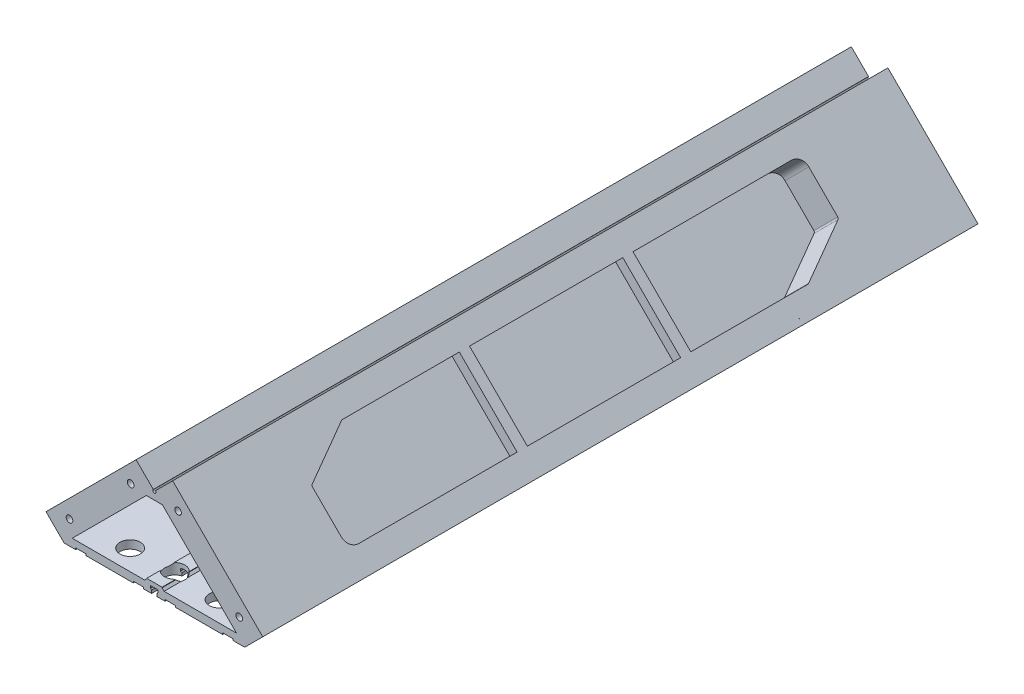
SolidWorks part; units mm, degrees
ref_plane "Front Plane" through (0, 0, 0) normal (0, 0, 1) x (1, 0, 0)
ref_plane "Top Plane" through (0, 0, 0) normal (0, 1, 0) x (1, 0, 0)
ref_plane "Right Plane" through (0, 0, 0) normal (1, 0, 0) x (0, 0, -1)
sketch "Sketch1" plane through (0, 0, 0) normal (0, 0, 1) x (1, 0, 0)
  line L0 (565, 0) -> (590, 0)
  line L1 (0, 0) -> (25, 0)
  line L2 (0, 0) -> (0, 950)
  line L4 (590, 0) -> (590, 950)
  line L5 (25, 55) -> (565, 55)
  line L6 (25, 55) -> (25, 895)
  line L7 (25, 920) -> (565, 920)
  line L8 (565, 55) -> (565, 895)
  line L10 (25, 0) -> (25, 30)
  line L11 (25, 30) -> (565, 30)
  line L12 (565, 0) -> (565, 30)
  line L13 (25, 895) -> (565, 895)
  line L14 (25, 920) -> (25, 950)
  line L15 (312.6777, 1262.6777) -> (630.8757, 944.4796)
  line L16 (295, 1280.3553) -> (312.6777, 1262.6777)
  line L17 (25, 975) -> (295, 1245)
  line L18 (565, 950) -> (565, 975)
  line L19 (565, 950) -> (565, 920)
  line L20 (590, 950) -> (613.1981, 926.8019)
  line L21 (25, 950) -> (25, 975)
  line L22 (295, 1280.3553) -> (277.3223, 1262.6777)
  line L23 (565, 975) -> (295, 1245)
  line L24 (277.3223, 1262.6777) -> (-40.8757, 944.4796)
  line L25 (-40.8757, 944.4796) -> (-23.1981, 926.8019)
  line L26 (0, 950) -> (-23.1981, 926.8019)
  line L27 (613.1981, 926.8019) -> (630.8757, 944.4796)
  line L28 (295, 1280.3553) -> (295, 1004.0858) construction
  point P9 (0, 475)
  dimension "D1" = 590
  dimension "D2" = 950
  dimension "D3" = 25
  dimension "D4" = 25
  dimension "D5" = 30
  dimension "D6" = 25
  dimension "D8" = 25
  dimension "D12" = 450
extrude "Boss-Extrude1" add sketch "Sketch1" along normal blind 25
sketch "Sketch2" plane through (0, 0, 25) normal (0, 0, 1) x (1, 0, 0)
  line L0 (0, 950) -> (0, 0) construction
  line L1 (25, 55) -> (0, 55)
  line L2 (25, 55) -> (25, 30)
  line L3 (25, 30) -> (0, 30)
  line L4 (0, 55) -> (0, 30)
  line L5 (590, 0) -> (590, 950) construction
  line L6 (565, 55) -> (590, 55)
  line L7 (565, 55) -> (565, 30)
  line L8 (565, 30) -> (590, 30)
  line L9 (590, 55) -> (590, 30)
  line L10 (295, 1280.3553) -> (312.6777, 1262.6777)
  line L11 (25, 920) -> (0, 920)
  line L12 (25, 920) -> (25, 895)
  line L13 (25, 895) -> (0, 895)
  line L14 (0, 920) -> (0, 895)
  line L15 (565, 920) -> (590, 920)
  line L16 (565, 920) -> (565, 895)
  line L17 (565, 895) -> (590, 895)
  line L18 (590, 920) -> (590, 895)
  line L20 (295, 1280.3553) -> (277.3223, 1262.6777)
  line L21 (295, 1245) -> (312.6777, 1262.6777)
  line L22 (295, 1245) -> (277.3223, 1262.6777)
  line L23 (295, 1277.5269) -> (309.8492, 1262.6777)
  line L24 (295, 1247.8284) -> (309.8492, 1262.6777)
  line L25 (295, 1247.8284) -> (280.1508, 1262.6777)
  line L26 (295, 1277.5269) -> (280.1508, 1262.6777)
  line L27 (23, 918) -> (2, 918)
  line L28 (2, 918) -> (2, 897)
  line L29 (23, 897) -> (2, 897)
  line L30 (23, 918) -> (23, 897)
  line L31 (567, 918) -> (588, 918)
  line L32 (588, 918) -> (588, 897)
  line L33 (567, 897) -> (588, 897)
  line L34 (567, 918) -> (567, 897)
  line L35 (23, 53) -> (2, 53)
  line L36 (2, 53) -> (2, 32)
  line L37 (23, 32) -> (2, 32)
  line L38 (23, 53) -> (23, 32)
  line L39 (567, 53) -> (588, 53)
  line L40 (588, 53) -> (588, 32)
  line L41 (567, 32) -> (588, 32)
  line L42 (567, 53) -> (567, 32)
  dimension "D1" = 2
  dimension "D2" = 2
  dimension "D3" = 2
  dimension "D4" = 2
  dimension "D5" = 2
extrude "Boss-Extrude2" add sketch "Sketch2" along normal blind 700
sketch "Sketch4" plane through (0, 0, 725) normal (0, 0, 1) x (1, 0, 0)
  line L2 (590, 895) -> (590, 920) construction
  line L9 (565, 895) -> (565, 55) construction
  line L11 (590, 55) -> (590, 895) construction
  line L18 (590, 30) -> (590, 55) construction
  line L21 (565, 30) -> (565, 0) construction
  line L22 (565, 0) -> (590, 0) construction
  line L23 (590, 0) -> (590, 30) construction
  line L25 (565, 55) -> (25, 55) construction
  line L27 (25, 30) -> (565, 30) construction
  line L29 (0, 30) -> (0, 0) construction
  line L30 (0, 0) -> (25, 0) construction
  line L31 (25, 0) -> (25, 30) construction
  line L34 (0, 55) -> (0, 30) construction
  line L41 (0, 895) -> (0, 55) construction
  line L43 (25, 55) -> (25, 895) construction
  line L46 (0, 920) -> (0, 895) construction
  line L53 (565, 920) -> (25, 920) construction
  line L55 (25, 895) -> (565, 895) construction
  line L57 (295, 1245) -> (565, 975) construction
  line L58 (565, 975) -> (565, 920) construction
  line L60 (590, 920) -> (590, 950) construction
  line L61 (590, 950) -> (613.1981, 926.8019) construction
  line L62 (613.1981, 926.8019) -> (630.8757, 944.4796) construction
  line L63 (630.8757, 944.4796) -> (312.6777, 1262.6777) construction
  line L64 (295, 1280.3553) -> (277.3223, 1262.6777) construction
  line L67 (312.6777, 1262.6777) -> (295, 1280.3553) construction
  line L73 (277.3223, 1262.6777) -> (-40.8757, 944.4796) construction
  line L74 (-40.8757, 944.4796) -> (-23.1981, 926.8019) construction
  line L75 (-23.1981, 926.8019) -> (0, 950) construction
  line L76 (0, 950) -> (0, 920) construction
  line L78 (25, 920) -> (25, 975) construction
  line L79 (25, 975) -> (295, 1245) construction
  line L82 (590, 895) -> (590, 920)
  line L89 (565, 895) -> (565, 55)
  line L91 (590, 55) -> (590, 895)
  line L98 (590, 30) -> (590, 55)
  line L101 (565, 30) -> (565, 0)
  line L102 (565, 0) -> (590, 0)
  line L103 (590, 0) -> (590, 30)
  line L105 (565, 55) -> (25, 55)
  line L107 (25, 30) -> (565, 30)
  line L109 (0, 30) -> (0, 0)
  line L110 (0, 0) -> (25, 0)
  line L111 (25, 0) -> (25, 30)
  line L114 (0, 55) -> (0, 30)
  line L121 (0, 895) -> (0, 55)
  line L123 (25, 55) -> (25, 895)
  line L126 (0, 920) -> (0, 895)
  line L133 (565, 920) -> (25, 920)
  line L135 (25, 895) -> (565, 895)
  line L137 (295, 1245) -> (565, 975)
  line L138 (565, 975) -> (565, 920)
  line L140 (590, 920) -> (590, 950)
  line L141 (590, 950) -> (613.1981, 926.8019)
  line L142 (613.1981, 926.8019) -> (630.8757, 944.4796)
  line L143 (630.8757, 944.4796) -> (312.6777, 1262.6777)
  line L144 (295, 1280.3553) -> (277.3223, 1262.6777)
  line L147 (312.6777, 1262.6777) -> (295, 1280.3553)
  line L153 (277.3223, 1262.6777) -> (-40.8757, 944.4796)
  line L154 (-40.8757, 944.4796) -> (-23.1981, 926.8019)
  line L155 (-23.1981, 926.8019) -> (0, 950)
  line L156 (0, 950) -> (0, 920)
  line L158 (25, 920) -> (25, 975)
  line L159 (25, 975) -> (295, 1245)
extrude "Boss-Extrude3" add sketch "Sketch4" along normal blind 25
sketch "Sketch6" plane through (0, 0, 0) normal (0, 0, -1) x (-1, 0, 0)
  line L0 (-25, 895) -> (-25, 55) construction
  line L1 (-25, 255) -> (-29, 255)
  line L2 (-25, 255) -> (-25, 275)
  line L3 (-25, 275) -> (-29, 275)
  line L4 (-29, 255) -> (-29, 275)
  line L5 (-25, 55) -> (-565, 55) construction
  line L6 (-25, 655) -> (-29, 655)
  line L7 (-25, 655) -> (-25, 675)
  line L8 (-25, 675) -> (-29, 675)
  line L9 (-29, 655) -> (-29, 675)
  line L10 (-295, 1280.3553) -> (-295, 1595.1993) construction
  line L11 (-561, 655) -> (-561, 675)
  line L12 (-565, 675) -> (-561, 675)
  line L13 (-565, 655) -> (-565, 675)
  line L14 (-565, 655) -> (-561, 655)
  line L15 (-561, 255) -> (-561, 275)
  line L16 (-565, 275) -> (-561, 275)
  line L17 (-565, 255) -> (-565, 275)
  line L18 (-565, 255) -> (-561, 255)
  dimension "D1" = 4
  dimension "D2" = 4
  dimension "D3" = 20
  dimension "D4" = 20
  dimension "D5" = 200
  dimension "D6" = 600
extrude "Boss-Extrude4" add sketch "Sketch6" against normal up to surface (25 mm away) up to face at (577.5, 475, 25)
sketch "Sketch8" plane through (0, 0, 750) normal (0, 0, 1) x (1, 0, 0)
  line L1 (29, 675) -> (25, 675)
  line L2 (29, 675) -> (29, 655)
  line L3 (29, 655) -> (25, 655)
  line L4 (25, 675) -> (25, 655)
  line L5 (29, 275) -> (25, 275)
  line L6 (29, 275) -> (29, 255)
  line L7 (29, 255) -> (25, 255)
  line L8 (25, 275) -> (25, 255)
  line L9 (561, 275) -> (565, 275)
  line L10 (561, 275) -> (561, 255)
  line L11 (561, 255) -> (565, 255)
  line L12 (565, 275) -> (565, 255)
  line L13 (561, 675) -> (565, 675)
  line L14 (561, 675) -> (561, 655)
  line L15 (561, 655) -> (565, 655)
  line L16 (565, 675) -> (565, 655)
extrude "Boss-Extrude5" add sketch "Sketch8" against normal up to surface (25 mm away) up to face at (577.5, 475, 725)
sketch "Sketch9" plane through (0, 0, 750) normal (0, 0, 1) x (1, 0, 0)
  line L0 (295, 1245) -> (295, 920) construction
  line L1 (561, 255) -> (551, 255)
  line L2 (561, 255) -> (561, 270)
  line L3 (561, 270) -> (559, 270)
  line L4 (551, 255) -> (551, 257)
  line L7 (551, 257) -> (559, 257)
  line L8 (559, 270) -> (559, 257)
  line L9 (561, 655) -> (551, 655)
  line L10 (561, 655) -> (561, 670)
  line L11 (561, 670) -> (559, 670)
  line L12 (551, 655) -> (551, 657)
  line L15 (551, 657) -> (559, 657)
  line L16 (559, 670) -> (559, 657)
  line L17 (25, 920) -> (565, 920) construction
  line L18 (31, 670) -> (31, 657)
  line L19 (39, 657) -> (31, 657)
  line L20 (39, 655) -> (39, 657)
  line L21 (29, 670) -> (31, 670)
  line L22 (29, 655) -> (29, 670)
  line L23 (29, 655) -> (39, 655)
  line L24 (31, 270) -> (31, 257)
  line L25 (39, 257) -> (31, 257)
  line L26 (39, 255) -> (39, 257)
  line L27 (29, 270) -> (31, 270)
  line L28 (29, 255) -> (29, 270)
  line L29 (29, 255) -> (39, 255)
  dimension "D1" = 15
  dimension "D2" = 10
  dimension "D3" = 8
  dimension "D4" = 13
  dimension "D5" = 10
  dimension "D6" = 15
  dimension "D7" = 13
  dimension "D8" = 8
extrude "Boss-Extrude6" add sketch "Sketch9" against normal up to surface (750 mm away) up to face at (295, 537.1476, 0)
sketch "Sketch10" plane through (0, 0, 0) normal (0, -1, 0) x (1, 0, 0)
  circle A0 centre (577.5, 12.5) radius 20
  circle A1 centre (577.5, 737.5) radius 20
  circle A2 centre (12.5, 737.5) radius 20
  circle A3 centre (12.5, 12.5) radius 20
  dimension "D1" = 40
extrude "Boss-Extrude7" add sketch "Sketch10" along normal blind 6
sketch "Sketch11" plane through (0, -6, 0) normal (0, -1, 0) x (1, 0, 0)
  line L0 (295, 25) -> (295, -142.0553) construction
  line L1 (591.3227, 25.9794) -> (563.3227, 25.9794)
  line L2 (591.3227, 25.9794) -> (591.3227, -19.0206)
  line L3 (591.3227, -19.0206) -> (563.3227, -19.0206)
  line L4 (563.3227, 25.9794) -> (563.3227, -19.0206)
  line L5 (563.3227, 724.0206) -> (563.3227, 769.0206)
  line L6 (591.3227, 769.0206) -> (563.3227, 769.0206)
  line L10 (591.3227, 724.0206) -> (591.3227, 769.0206)
  line L11 (591.3227, 724.0206) -> (563.3227, 724.0206)
  line L12 (25, 25) -> (565, 25) construction
  line L13 (-1.3227, 724.0206) -> (26.6773, 724.0206)
  line L14 (-1.3227, 724.0206) -> (-1.3227, 769.0206)
  line L15 (-1.3227, 769.0206) -> (26.6773, 769.0206)
  line L16 (26.6773, 724.0206) -> (26.6773, 769.0206)
  line L17 (26.6773, 25.9794) -> (26.6773, -19.0206)
  line L18 (-1.3227, -19.0206) -> (26.6773, -19.0206)
  line L19 (-1.3227, 25.9794) -> (-1.3227, -19.0206)
  line L20 (-1.3227, 25.9794) -> (26.6773, 25.9794)
  dimension "D1" = 28
  dimension "D2" = 45
extrude "Boss-Extrude8" add sketch "Sketch11" along normal blind 2
sketch "Sketch12" plane through (0, -8, 0) normal (0, -1, 0) x (1, 0, 0)
  line L0 (591.3227, -19.0206) -> (591.3227, 25.9794) construction
  line L1 (591.3227, 25.9794) -> (589.3227, 25.9794)
  line L2 (591.3227, 25.9794) -> (591.3227, -19.0206)
  line L3 (591.3227, -19.0206) -> (589.3227, -19.0206)
  line L4 (589.3227, 25.9794) -> (589.3227, -19.0206)
  line L5 (591.3227, 25.9794) -> (563.3227, 25.9794) construction
  line L6 (563.3227, -19.0206) -> (591.3227, -19.0206) construction
  line L7 (590, 375) -> (666.7181, 375) construction
  line L8 (563.3227, 25.9794) -> (565.3227, 25.9794)
  line L9 (563.3227, 25.9794) -> (563.3227, -19.0206)
  line L10 (563.3227, -19.0206) -> (565.3227, -19.0206)
  line L11 (565.3227, 25.9794) -> (565.3227, -19.0206)
  line L13 (24.6773, 25.9794) -> (24.6773, -19.0206)
  line L14 (26.6773, -19.0206) -> (24.6773, -19.0206)
  line L15 (26.6773, 25.9794) -> (26.6773, -19.0206)
  line L16 (26.6773, 25.9794) -> (24.6773, 25.9794)
  line L17 (0.6773, 25.9794) -> (0.6773, -19.0206)
  line L18 (-1.3227, -19.0206) -> (0.6773, -19.0206)
  line L19 (-1.3227, 25.9794) -> (-1.3227, -19.0206)
  line L20 (-1.3227, 25.9794) -> (0.6773, 25.9794)
  line L21 (590, 725) -> (590, 25) construction
  line L22 (-1.3227, 724.0206) -> (0.6773, 724.0206)
  line L23 (-1.3227, 724.0206) -> (-1.3227, 769.0206)
  line L24 (-1.3227, 769.0206) -> (0.6773, 769.0206)
  line L25 (0.6773, 724.0206) -> (0.6773, 769.0206)
  line L26 (26.6773, 724.0206) -> (24.6773, 724.0206)
  line L27 (26.6773, 724.0206) -> (26.6773, 769.0206)
  line L28 (26.6773, 769.0206) -> (24.6773, 769.0206)
  line L29 (24.6773, 724.0206) -> (24.6773, 769.0206)
  line L30 (565.3227, 724.0206) -> (565.3227, 769.0206)
  line L31 (563.3227, 769.0206) -> (565.3227, 769.0206)
  line L32 (563.3227, 724.0206) -> (563.3227, 769.0206)
  line L33 (563.3227, 724.0206) -> (565.3227, 724.0206)
  line L34 (589.3227, 724.0206) -> (589.3227, 769.0206)
  line L35 (591.3227, 769.0206) -> (589.3227, 769.0206)
  line L36 (591.3227, 724.0206) -> (591.3227, 769.0206)
  line L37 (591.3227, 724.0206) -> (589.3227, 724.0206)
  dimension "D1" = 2
  dimension "D2" = 2
extrude "Boss-Extrude9" add sketch "Sketch12" along normal blind 38
sketch "Sketch13" plane through (591.3227, 0, 0) normal (1, 0, 0) x (0, 0, -1)
  line L0 (-25.9794, -6) -> (9.0206, -46)
  line L1 (19.0206, -46) -> (-25.9794, -46) construction
  line L2 (19.0206, -46) -> (19.0206, -6) construction
  line L3 (9.0206, -46) -> (-32.8867, -57.1167)
  line L4 (-32.8867, -57.1167) -> (-25.9794, -6)
  line L5 (-375, 30) -> (-375, -46) construction
  line L6 (-725, 30) -> (-25, 30) construction
  line L7 (-717.1133, -57.1167) -> (-724.0206, -6)
  line L8 (-759.0206, -46) -> (-717.1133, -57.1167)
  line L9 (-724.0206, -6) -> (-759.0206, -46)
  dimension "D1" = 10
extrude "Cut-Extrude1" cut sketch "Sketch13" against normal through all
fillet "Fillet1" radius 6 16 edges at (590.3227, -46, 759.0206) (590.3227, -46, 769.0206) (-0.3227, -46, -9.0206) (-0.3227, -46, -19.0206) (25.6773, -46, -19.0206) (25.6773, -46, -9.0206) (25.6773, -46, 759.0206) (-0.3227, -46, 759.0206) (-0.3227, -46, 769.0206) (25.6773, -46, 769.0206) (564.3227, -46, 759.0206) (564.3227, -46, 769.0206) (590.3227, -46, -19.0206) (564.3227, -46, -19.0206) (564.3227, -46, -9.0206) (590.3227, -46, -9.0206)
sketch "Sketch14" plane through (565.3227, 0, 0) normal (1, 0, 0) x (0, 0, -1)
  circle A0 centre (13.0206, -40) radius 25
  circle A1 centre (-763.0206, -40) radius 25
  dimension "D1" = 50
  dimension "D2" = 50
extrude "Boss-Extrude10" add sketch "Sketch14" along normal up to surface (24 mm away) up to face at (589.3227, -32.2803, -7.8041)
sketch "Sketch15" plane through (24.6773, 0, 0) normal (-1, 0, 0) x (0, 0, 1)
  circle A0 centre (763.0206, -40) radius 25
  circle A1 centre (-13.0206, -40) radius 25
extrude "Boss-Extrude11" add sketch "Sketch15" along normal up to surface (24 mm away) up to face at (0.6773, -32.2803, -7.8041)
sketch "Sketch18" plane through (0, 0, 25) normal (0, 0, 1) x (1, 0, 0)
  line L0 (277.1102, 1262.4655) -> (188.934, 1174.2893)
  line L1 (295, 1280.3553) -> (-40.8757, 944.4796) construction
  line L2 (312.8898, 1262.4655) -> (401.066, 1174.2893)
  line L3 (293.9393, 1245.6364) -> (277.1102, 1262.4655)
  line L4 (630.8757, 944.4796) -> (295, 1280.3553) construction
  line L5 (401.066, 1174.2893) -> (383.3883, 1156.6117)
  line L6 (565, 975) -> (295, 1245) construction
  line L7 (188.934, 1174.2893) -> (206.6117, 1156.6117)
  line L8 (295, 1245) -> (25, 975) construction
  line L9 (206.6117, 1156.6117) -> (383.3883, 1156.6117)
  line L10 (277.1102, 1255.3945) -> (196.0051, 1174.2893)
  line L11 (196.0051, 1174.2893) -> (205.6827, 1164.6117)
  line L12 (296.0607, 1245.6364) -> (312.8898, 1262.4655)
  line L14 (393.9949, 1174.2893) -> (384.3173, 1164.6117)
  line L15 (312.8898, 1255.3945) -> (393.9949, 1174.2893)
  line L16 (295, 1237.5047) -> (312.8898, 1255.3945)
  line L17 (295, 1237.5047) -> (277.1102, 1255.3945)
  line L18 (196.0051, 1174.2893) -> (208.6827, 1161.6117) construction
  line L19 (384.3173, 1164.6117) -> (205.6827, 1164.6117)
  line L20 (393.9949, 1174.2893) -> (381.3173, 1161.6117) construction
  line L21 (208.6827, 1161.6117) -> (381.3173, 1161.6117) construction
  line L22 (295, 1244.5757) -> (312.8898, 1262.4655) construction
  line L23 (295, 1244.5757) -> (277.1102, 1262.4655) construction
  arc A0 (293.9393, 1245.6364) -> (296.0607, 1245.6364) centre (295, 1244.5757) ccw
  dimension "D2" = 3
  dimension "D1" = 5
extrude "Boss-Extrude13" add sketch "Sketch18" along normal up to surface (700 mm away) up to face at (520.2189, 1017.9949, 725)
sketch "Sketch19" plane through (0, 0, 0) normal (0, 0, -1) x (-1, 0, 0)
  line L0 (-401.066, 1174.2893) -> (-312.8898, 1262.4655)
  line L1 (-312.8898, 1262.4655) -> (-296.0607, 1245.6364)
  line L2 (-293.9393, 1245.6364) -> (-277.1102, 1262.4655)
  line L3 (-277.1102, 1262.4655) -> (-188.934, 1174.2893)
  line L4 (-188.934, 1174.2893) -> (-206.6117, 1156.6117)
  line L5 (-206.6117, 1156.6117) -> (-383.3883, 1156.6117)
  line L6 (-383.3883, 1156.6117) -> (-401.066, 1174.2893)
  arc A0 (-296.0607, 1245.6364) -> (-293.9393, 1245.6364) centre (-295, 1244.5757) ccw
extrude "Cut-Extrude2" cut sketch "Sketch19" against normal through all flip side to cut
sketch "Sketch20" plane through (0, 0, 0) normal (0, 0, -1) x (-1, 0, 0)
  circle A0 centre (-293.0221, 1200.6008) radius 150.3669
extrude "Cut-Extrude3" cut sketch "Sketch20" against normal blind 25
sketch "Sketch21" plane through (0, 0, 750) normal (0, 0, 1) x (1, 0, 0)
  circle A0 centre (288.0844, 1190.2881) radius 126.6007
extrude "Cut-Extrude4" cut sketch "Sketch21" against normal blind 25
sketch "Sketch22" plane through (0, 0, 0) normal (0, 0, 1) x (1, 0, 0)
  circle A0 centre (322.4016, 0) radius 452.2192
extrude "Cut-Extrude5" cut sketch "Sketch22" against normal through all
sketch "Sketch25" plane through (0, 0, 25) normal (0, 0, -1) x (-1, 0, 0)
  line L0 (-295, 1237.5047) -> (-295, 1156.6117) construction
  line L1 (-206.6117, 1156.6117) -> (-383.3883, 1156.6117) construction
  line L16 (-371.9832, 1155.1117) -> (-361.7832, 1155.1117)
  line L17 (-371.9832, 1155.1117) -> (-371.9832, 1158.1117)
  line L18 (-371.9832, 1158.1117) -> (-361.7832, 1158.1117)
  line L19 (-361.7832, 1155.1117) -> (-361.7832, 1158.1117)
  line L31 (-315.6596, 1155.1117) -> (-305.4596, 1155.1117)
  line L32 (-315.6596, 1155.1117) -> (-315.6596, 1158.1117)
  line L33 (-315.6596, 1158.1117) -> (-305.4596, 1158.1117)
  line L34 (-305.4596, 1155.1117) -> (-305.4596, 1158.1117)
  line L38 (-284.5404, 1155.1117) -> (-284.5404, 1158.1117)
  line L39 (-274.3404, 1158.1117) -> (-284.5404, 1158.1117)
  line L40 (-274.3404, 1155.1117) -> (-274.3404, 1158.1117)
  line L41 (-274.3404, 1155.1117) -> (-284.5404, 1155.1117)
  line L42 (-228.2168, 1155.1117) -> (-228.2168, 1158.1117)
  line L43 (-218.0168, 1158.1117) -> (-228.2168, 1158.1117)
  line L44 (-218.0168, 1155.1117) -> (-218.0168, 1158.1117)
  line L45 (-218.0168, 1155.1117) -> (-228.2168, 1155.1117)
  dimension "D1" = 10.2
  dimension "D2" = 10.2
  dimension "D3" = 3
  dimension "D4" = 3
extrude "Cut-Extrude7" cut sketch "Sketch25" against normal through all
sketch "Sketch28" plane through (0, 0, 25) normal (0, 0, -1) x (-1, 0, 0)
  line L0 (-284.5404, 1156.6117) -> (-305.4596, 1156.6117) construction
  line L5 (-297.7, 1153.4117) -> (-292.3, 1153.4117)
  line L6 (-292.3, 1153.4117) -> (-292.3, 1159.5288)
  line L12 (-292.3, 1159.5288) -> (-291.3, 1160.5288)
  line L13 (-291.3, 1160.5288) -> (-291.3, 1162.8117)
  line L15 (-291.3, 1162.8117) -> (-298.7, 1162.8117)
  line L16 (-298.7, 1160.5288) -> (-298.7, 1162.8117)
  line L17 (-297.7, 1159.5288) -> (-298.7, 1160.5288)
  line L18 (-297.7, 1153.4117) -> (-297.7, 1159.5288)
  point P0 (-295, 1156.6117)
  point P7 (-295, 1159.6117)
extrude "Cut-Extrude8" cut sketch "Sketch28" against normal through all
sketch "Sketch32" plane through (0, 0, 25) normal (0, 0, -1) x (-1, 0, 0)
  line L0 (-205.6827, 1164.6117) -> (-384.3173, 1164.6117) construction
  line L1 (-302.5, 1167.1117) -> (-287.5, 1167.1117)
  line L2 (-302.5, 1167.1117) -> (-302.5, 1164.6117)
  line L4 (-287.5, 1167.1117) -> (-287.5, 1164.6117)
  line L5 (-302.5, 1167.1117) -> (-295, 1164.6117) construction
  line L6 (-295, 1164.6117) -> (-287.5, 1167.1117) construction
  line L7 (-302.5, 1164.6117) -> (-287.5, 1164.6117)
  point P0 (-295, 1164.6117)
  dimension "D1" = 15
extrude "Boss-Extrude15" add sketch "Sketch32" against normal up to surface (700 mm away) up to face at (295, 1171.006, 725)
chamfer "Chamfer1" distance 2 angle 45 1 edges at (302.5, 1164.6117, 375)
chamfer "Chamfer2" distance 2 angle 45 1 edges at (287.5, 1164.6117, 375)
sketch "Sketch36" plane through (0, 0, 25) normal (0, 0, -1) x (-1, 0, 0)
  line L0 (-291.204, 1245.1087) -> (-287.5, 1245.1087)
  line L5 (-302.5, 1245.1087) -> (-298.796, 1245.1087)
  line L6 (-302.5, 1245.1087) -> (-302.5, 1237.1087)
  line L7 (-302.5, 1237.1087) -> (-287.5, 1237.1087)
  line L8 (-287.5, 1245.1087) -> (-287.5, 1237.1087)
  line L9 (-298.4776, 1242.9634) -> (-294.4016, 1240.7895) construction
  line L10 (-295.5984, 1240.7895) -> (-287.5, 1245.1087) construction
  arc A0 (-298.796, 1245.1087) -> (-291.204, 1245.1087) centre (-295, 1244.5757) ccw
  point P0 (-295, 1241.1087)
  dimension "D1" = 15
  dimension "D2" = 8
extrude "Boss-Extrude16" add sketch "Sketch36" against normal up to surface (700 mm away) up to face at (295, 1171.006, 725)
sketch "Sketch38" plane through (787.6777, 787.6777, 0) normal (0.7071, 0.7071, 0) x (0, 0, -1)
  line L0 (-725, 671.4514) -> (-25, 671.4514) construction
  line L1 (-575, 649.4514) -> (-135, 649.4514)
  line L2 (-625, 620.5839) -> (-625, 579.4514)
  line L3 (-615, 569.4514) -> (-175, 569.4514)
  line L4 (-125, 639.4514) -> (-125, 598.319)
  line L6 (-575, 649.4514) -> (-625, 620.5839)
  line L7 (-125, 598.319) -> (-175, 569.4514)
  arc A0 (-125, 639.4514) -> (-135, 649.4514) centre (-135, 639.4514) ccw
  arc A1 (-615, 569.4514) -> (-625, 579.4514) centre (-615, 579.4514) cw
  dimension "D2" = 10
  dimension "D1" = 100
  dimension "D4" = 22
  dimension "D5" = 30
  dimension "D8" = 30
extrude "Cut-Extrude12" cut sketch "Sketch38" against normal blind 6
sketch "Sketch39" plane through (787.6777, 787.6777, 0) normal (0.7071, 0.7071, 0) x (0, 0, -1)
  line L0 (-125, 598.319) -> (-125, 639.4514) construction
  line L1 (-175, 569.4514) -> (-125, 598.319) construction
  line L2 (-615, 569.4514) -> (-175, 569.4514) construction
  line L3 (-625, 620.5839) -> (-625, 579.4514) construction
  line L4 (-575, 649.4514) -> (-625, 620.5839) construction
  line L5 (-135, 649.4514) -> (-575, 649.4514) construction
  line L6 (-125, 598.319) -> (-125, 639.4514)
  line L7 (-175, 569.4514) -> (-125, 598.319)
  line L8 (-615, 569.4514) -> (-175, 569.4514)
  line L9 (-625, 620.5839) -> (-625, 579.4514)
  line L10 (-575, 649.4514) -> (-625, 620.5839)
  line L11 (-135, 649.4514) -> (-575, 649.4514)
  line L12 (-121, 596.0096) -> (-121, 639.4514)
  line L13 (-135, 653.4514) -> (-576.0718, 653.4514)
  line L14 (-576.0718, 653.4514) -> (-629, 622.8933)
  line L15 (-629, 622.8933) -> (-629, 579.4514)
  line L16 (-615, 565.4514) -> (-173.9282, 565.4514)
  line L17 (-173.9282, 565.4514) -> (-121, 596.0096)
  arc A0 (-125, 639.4514) -> (-135, 649.4514) centre (-135, 639.4514) ccw construction
  arc A1 (-625, 579.4514) -> (-615, 569.4514) centre (-615, 579.4514) ccw construction
  arc A2 (-125, 639.4514) -> (-135, 649.4514) centre (-135, 639.4514) ccw
  arc A3 (-625, 579.4514) -> (-615, 569.4514) centre (-615, 579.4514) ccw
  arc A4 (-121, 639.4514) -> (-135, 653.4514) centre (-135, 639.4514) ccw
  arc A5 (-629, 579.4514) -> (-615, 565.4514) centre (-615, 579.4514) ccw
  dimension "D1" = 4
extrude "Boss-Extrude17" add sketch "Sketch39" against normal blind 33
sketch "Sketch40" plane through (764.3431, 764.3431, 0) normal (-0.7071, -0.7071, 0) x (0, 0, 1)
  line L6 (172.8652, 566.0652) -> (619.0997, 566.0652)
  line L7 (629, 579.4514) -> (629, 622.8933)
  line L8 (629, 622.8933) -> (576.0718, 653.4514)
  line L9 (576.0718, 653.4514) -> (135, 653.4514)
  line L10 (121, 639.4514) -> (121, 596.0096)
  line L11 (121, 596.0096) -> (172.8652, 566.0652)
  line L12 (172.8652, 566.0652) -> (619.0997, 566.0652)
  line L13 (629, 579.4514) -> (629, 622.8933)
  line L14 (629, 622.8933) -> (576.0718, 653.4514)
  line L15 (576.0718, 653.4514) -> (135, 653.4514)
  line L16 (121, 639.4514) -> (121, 596.0096)
  line L17 (121, 596.0096) -> (172.8652, 566.0652)
  arc A2 (619.0997, 566.0652) -> (629, 579.4514) centre (615, 579.4514) ccw
  arc A3 (135, 653.4514) -> (121, 639.4514) centre (135, 639.4514) ccw
  arc A4 (619.0997, 566.0652) -> (629, 579.4514) centre (615, 579.4514) ccw
  arc A5 (135, 653.4514) -> (121, 639.4514) centre (135, 639.4514) ccw
  dimension "D1" = 0
extrude "Boss-Extrude18" add sketch "Sketch40" along normal blind 4
fillet "Fillet2" radius 2 4 edges at (373.3474, 1178.6734, 175) (352.935, 1199.0858, 125) (316.7789, 1235.2419, 575) (337.1913, 1214.8295, 625)
sketch "Sketch42" plane through (-492.6777, 492.6777, 0) normal (-0.7071, 0.7071, 0) x (0, 0, 1)
  line L1 (175, 1066.6444) -> (615, 1066.6444)
  line L2 (125, 1037.7769) -> (125, 996.6444)
  line L3 (135, 986.6444) -> (575, 986.6444)
  line L4 (625, 1056.6444) -> (625, 1015.512)
  line L5 (25, 963.9444) -> (25, 1088.6444) construction
  line L6 (175, 1066.6444) -> (125, 1037.7769)
  line L7 (625, 1015.512) -> (575, 986.6444)
  line L9 (725, 1088.6444) -> (25, 1088.6444) construction
  arc A0 (625, 1056.6444) -> (615, 1066.6444) centre (615, 1056.6444) ccw
  arc A1 (135, 986.6444) -> (125, 996.6444) centre (135, 996.6444) cw
  dimension "D2" = 10
  dimension "D1" = 440
  dimension "D3" = 80
  dimension "D4" = 500
  dimension "D5" = 30
  dimension "D6" = 57.735
  dimension "D7" = 100
  dimension "D8" = 30
  dimension "D9" = 22
extrude "Cut-Extrude13" cut sketch "Sketch42" against normal blind 10
sketch "Sketch43" plane through (-492.6777, 492.6777, 0) normal (-0.7071, 0.7071, 0) x (0, 0, 1)
  line L0 (615, 1070.6444) -> (173.9282, 1070.6444)
  line L1 (173.9282, 1070.6444) -> (121, 1040.0863)
  line L2 (121, 1040.0863) -> (121, 996.6444)
  line L3 (135, 982.6444) -> (576.0718, 982.6444)
  line L4 (576.0718, 982.6444) -> (629, 1013.2026)
  line L5 (629, 1013.2026) -> (629, 1056.6444)
  line L6 (615, 1066.6444) -> (175, 1066.6444)
  line L7 (625, 1015.512) -> (625, 1056.6444)
  line L8 (575, 986.6444) -> (625, 1015.512)
  line L9 (135, 986.6444) -> (575, 986.6444)
  line L10 (125, 1037.7769) -> (125, 996.6444)
  line L11 (175, 1066.6444) -> (125, 1037.7769)
  line L12 (615, 1066.6444) -> (175, 1066.6444)
  line L13 (625, 1015.512) -> (625, 1056.6444)
  line L14 (575, 986.6444) -> (625, 1015.512)
  line L15 (135, 986.6444) -> (575, 986.6444)
  line L16 (125, 1037.7769) -> (125, 996.6444)
  line L17 (175, 1066.6444) -> (125, 1037.7769)
  arc A0 (121, 996.6444) -> (135, 982.6444) centre (135, 996.6444) ccw
  arc A1 (629, 1056.6444) -> (615, 1070.6444) centre (615, 1056.6444) ccw
  arc A2 (625, 1056.6444) -> (615, 1066.6444) centre (615, 1056.6444) ccw
  arc A3 (125, 996.6444) -> (135, 986.6444) centre (135, 996.6444) ccw
  arc A4 (625, 1056.6444) -> (615, 1066.6444) centre (615, 1056.6444) ccw
  arc A5 (125, 996.6444) -> (135, 986.6444) centre (135, 996.6444) ccw
  dimension "D1" = 0
  dimension "D2" = 4
extrude "Boss-Extrude19" add sketch "Sketch43" against normal blind 33
sketch "Sketch44" plane through (-469.3431, 469.3431, 0) normal (0.7071, -0.7071, 0) x (0, 0, -1)
  line L6 (-577.1348, 983.2582) -> (-130.9003, 983.2582)
  line L7 (-121, 996.6444) -> (-121, 1040.0863)
  line L8 (-121, 1040.0863) -> (-173.9282, 1070.6444)
  line L9 (-173.9282, 1070.6444) -> (-615, 1070.6444)
  line L10 (-629, 1056.6444) -> (-629, 1013.2026)
  line L11 (-629, 1013.2026) -> (-577.1348, 983.2582)
  line L12 (-577.1348, 983.2582) -> (-130.9003, 983.2582)
  line L13 (-121, 996.6444) -> (-121, 1040.0863)
  line L14 (-121, 1040.0863) -> (-173.9282, 1070.6444)
  line L15 (-173.9282, 1070.6444) -> (-615, 1070.6444)
  line L16 (-629, 1056.6444) -> (-629, 1013.2026)
  line L17 (-629, 1013.2026) -> (-577.1348, 983.2582)
  arc A2 (-130.9003, 983.2582) -> (-121, 996.6444) centre (-135, 996.6444) ccw
  arc A3 (-615, 1070.6444) -> (-629, 1056.6444) centre (-615, 1056.6444) ccw
  arc A4 (-130.9003, 983.2582) -> (-121, 996.6444) centre (-135, 996.6444) ccw
  arc A5 (-615, 1070.6444) -> (-629, 1056.6444) centre (-615, 1056.6444) ccw
  dimension "D1" = 0
extrude "Boss-Extrude20" add sketch "Sketch44" along normal blind 4
sketch "Sketch46" plane through (787.6777, 787.6777, 0) normal (0.7071, 0.7071, 0) x (0, 0, -1)
  line L0 (-135, 659.4514) -> (-577.6795, 659.4514)
  line L1 (-577.6795, 659.4514) -> (-635, 626.3574)
  line L2 (-635, 626.3574) -> (-635, 579.4514)
  line L3 (-615, 559.4514) -> (-172.3205, 559.4514)
  line L4 (-172.3205, 559.4514) -> (-115, 592.5455)
  line L5 (-115, 592.5455) -> (-115, 639.4514)
  line L6 (-135, 649.4514) -> (-575, 649.4514)
  line L7 (-125, 598.319) -> (-125, 639.4514)
  line L8 (-175, 569.4514) -> (-125, 598.319)
  line L9 (-615, 569.4514) -> (-175, 569.4514)
  line L10 (-625, 620.5839) -> (-625, 579.4514)
  line L11 (-575, 649.4514) -> (-625, 620.5839)
  line L12 (-135, 649.4514) -> (-575, 649.4514)
  line L13 (-125, 598.319) -> (-125, 639.4514)
  line L14 (-175, 569.4514) -> (-125, 598.319)
  line L15 (-615, 569.4514) -> (-175, 569.4514)
  line L16 (-625, 620.5839) -> (-625, 579.4514)
  line L17 (-575, 649.4514) -> (-625, 620.5839)
  arc A0 (-635, 579.4514) -> (-615, 559.4514) centre (-615, 579.4514) ccw
  arc A1 (-115, 639.4514) -> (-135, 659.4514) centre (-135, 639.4514) ccw
  arc A2 (-125, 639.4514) -> (-135, 649.4514) centre (-135, 639.4514) ccw
  arc A3 (-625, 579.4514) -> (-615, 569.4514) centre (-615, 579.4514) ccw
  arc A4 (-125, 639.4514) -> (-135, 649.4514) centre (-135, 639.4514) ccw
  arc A5 (-625, 579.4514) -> (-615, 569.4514) centre (-615, 579.4514) ccw
  dimension "D1" = 0
  dimension "D2" = 10
extrude "Boss-Extrude21" add sketch "Sketch46" against normal blind 10
sketch "Sketch47" plane through (-492.6777, 492.6777, 0) normal (-0.7071, 0.7071, 0) x (0, 0, 1)
  line L0 (615, 1076.6444) -> (172.3205, 1076.6444)
  line L1 (172.3205, 1076.6444) -> (115, 1043.5504)
  line L2 (115, 1043.5504) -> (115, 996.6444)
  line L3 (135, 976.6444) -> (577.6795, 976.6444)
  line L4 (577.6795, 976.6444) -> (635, 1009.7385)
  line L5 (635, 1009.7385) -> (635, 1056.6444)
  line L6 (615, 1066.6444) -> (175, 1066.6444)
  line L7 (625, 1015.512) -> (625, 1056.6444)
  line L8 (575, 986.6444) -> (625, 1015.512)
  line L9 (135, 986.6444) -> (575, 986.6444)
  line L10 (125, 1037.7769) -> (125, 996.6444)
  line L11 (175, 1066.6444) -> (125, 1037.7769)
  line L12 (615, 1066.6444) -> (175, 1066.6444)
  line L13 (625, 1015.512) -> (625, 1056.6444)
  line L14 (575, 986.6444) -> (625, 1015.512)
  line L15 (135, 986.6444) -> (575, 986.6444)
  line L16 (125, 1037.7769) -> (125, 996.6444)
  line L17 (175, 1066.6444) -> (125, 1037.7769)
  arc A0 (115, 996.6444) -> (135, 976.6444) centre (135, 996.6444) ccw
  arc A1 (635, 1056.6444) -> (615, 1076.6444) centre (615, 1056.6444) ccw
  arc A2 (625, 1056.6444) -> (615, 1066.6444) centre (615, 1056.6444) ccw
  arc A3 (125, 996.6444) -> (135, 986.6444) centre (135, 996.6444) ccw
  arc A4 (625, 1056.6444) -> (615, 1066.6444) centre (615, 1056.6444) ccw
  arc A5 (125, 996.6444) -> (135, 986.6444) centre (135, 996.6444) ccw
  dimension "D1" = 0
  dimension "D2" = 10
extrude "Boss-Extrude22" add sketch "Sketch47" against normal blind 10
sketch "Sketch48" plane through (0, 1156.6117, 0) normal (0, -1, 0) x (1, 0, 0)
  line L0 (291.3, 725) -> (298.7, 725) construction
  line L3 (188.934, 375) -> (137.9031, 375) construction
  circle A0 centre (295, 705) radius 10
  circle A1 centre (338.72, 705) radius 10
  circle A2 centre (251.2786, 705) radius 10
  circle A3 centre (251.2786, 45) radius 10
  circle A4 centre (338.72, 45) radius 10
  circle A5 centre (295, 45) radius 10
  dimension "D1" = 20
  dimension "D3" = 43.7214
  dimension "D2" = 20
  dimension "D4" = 43.72
extrude "Cut-Extrude14" cut sketch "Sketch48" against normal blind 20
sketch "Sketch49" plane through (-459.2315, 459.2315, 0) normal (0.7071, -0.7071, 0) x (0, 0, -1)
  line L0 (-135, 1080.9444) -> (-574.4641, 1080.9444) construction
  line L1 (-529.7321, 1080.9444) -> (-179.7321, 1080.9444)
  line L2 (-529.7321, 1080.9444) -> (-529.7321, 1085.9444)
  line L3 (-529.7321, 1085.9444) -> (-179.7321, 1085.9444)
  line L4 (-179.7321, 1080.9444) -> (-179.7321, 1085.9444)
  point P12 (0, 0)
  dimension "D1" = 5
  dimension "D2" = 350
extrude "Cut-Extrude15" cut sketch "Sketch49" against normal blind 10
fillet "Fillet3" radius 2 4 edges at (307.2329, 1228.5244, 529.7321) (307.2329, 1228.5244, 179.7321) (303.6974, 1224.9889, 179.7321) (303.6974, 1224.9889, 529.7321)
sketch "Sketch50" plane through (754.2315, 754.2315, 0) normal (-0.7071, -0.7071, 0) x (0, 0, 1)
  line L0 (615, 663.7514) -> (175, 663.7514) construction
  line L1 (220, 663.7514) -> (570, 663.7514)
  line L2 (220, 663.7514) -> (220, 668.7514)
  line L3 (220, 668.7514) -> (570, 668.7514)
  line L4 (570, 663.7514) -> (570, 668.7514)
  point P12 (0, 0)
  dimension "D1" = 350
  dimension "D2" = 5
extrude "Cut-Extrude16" cut sketch "Sketch50" against normal blind 10
fillet "Fillet4" radius 2 4 edges at (282.7671, 1228.5244, 220) (282.7671, 1228.5244, 570) (286.3026, 1224.9889, 570) (286.3026, 1224.9889, 220)
sketch "Sketch51" plane through (-492.6777, 492.6777, 0) normal (-0.7071, 0.7071, 0) x (0, 0, 1)
  line L0 (290, 1066.6444) -> (300, 1066.6444)
  line L2 (290, 986.6444) -> (300, 986.6444)
  line L4 (300, 1066.6444) -> (300, 986.6444)
  line L5 (615, 1066.6444) -> (175, 1066.6444) construction
  line L6 (135, 986.6444) -> (575, 986.6444) construction
  line L7 (290, 1066.6444) -> (290, 986.6444)
  line L8 (450, 1066.6444) -> (450, 986.6444)
  line L9 (460, 1066.6444) -> (460, 986.6444)
  line L10 (125, 1037.7769) -> (125, 996.6444) construction
  line L11 (450, 1066.6444) -> (460, 1066.6444)
  line L12 (450, 986.6444) -> (460, 986.6444)
  line L13 (625, 1015.512) -> (625, 1056.6444) construction
  point P2 (125, 1017.2107)
  dimension "D1" = 10
  dimension "D2" = 10
  dimension "D3" = 165
  dimension "D4" = 165
extrude "Boss-Extrude23" add sketch "Sketch51" against normal blind 10
sketch "Sketch53" plane through (787.6777, 787.6777, 0) normal (0.7071, 0.7071, 0) x (0, 0, -1)
  line L0 (-135, 649.4514) -> (-574.4641, 649.4514) construction
  line L1 (-460, 649.4514) -> (-450, 649.4514)
  line L2 (-460, 649.4514) -> (-460, 569.4514)
  line L3 (-460, 569.4514) -> (-450, 569.4514)
  line L4 (-450, 649.4514) -> (-450, 569.4514)
  line L5 (-615, 569.4514) -> (-175.5359, 569.4514) construction
  line L6 (-290, 686.7514) -> (-290, 696.7514) construction
  line L7 (-290, 649.4514) -> (-300, 649.4514)
  line L8 (-290, 649.4514) -> (-290, 569.4514)
  line L9 (-290, 569.4514) -> (-300, 569.4514)
  line L10 (-300, 649.4514) -> (-300, 569.4514)
  line L11 (-450, 686.7514) -> (-450, 696.7514) construction
  dimension "D1" = 10
  dimension "D2" = 10
extrude "Boss-Extrude24" add sketch "Sketch53" against normal blind 10
sketch "Sketch55" plane through (0, 0, 725) normal (0, 0, 1) x (1, 0, 0)
  line L0 (312.8898, 1262.4655) -> (296.8409, 1246.4166)
  line L1 (312.8898, 1262.4655) -> (296.0607, 1245.6364) construction
  line L2 (296.8409, 1243.1591) -> (383.3883, 1156.6117)
  line L3 (383.3883, 1156.6117) -> (401.066, 1174.2893) construction
  line L4 (383.3883, 1156.6117) -> (401.066, 1174.2893)
  line L5 (401.066, 1174.2893) -> (312.8898, 1262.4655)
  line L6 (295, 1162.8117) -> (295, 1181.0913) construction
  line L8 (291.3, 1162.8117) -> (298.7, 1162.8117) construction
  line L9 (188.934, 1174.2893) -> (277.1102, 1262.4655)
  line L10 (206.6117, 1156.6117) -> (188.934, 1174.2893)
  line L11 (293.1591, 1243.1591) -> (206.6117, 1156.6117)
  line L12 (277.1102, 1262.4655) -> (293.1591, 1246.4166)
  arc A0 (296.8409, 1243.1591) -> (296.8409, 1246.4166) centre (295.2121, 1244.7879) ccw
  arc A1 (293.1591, 1243.1591) -> (293.1591, 1246.4166) centre (294.7879, 1244.7879) cw
  dimension "D1" = 25
extrude "Boss-Extrude25" add sketch "Sketch55" against normal blind 15
sketch "Sketch56" plane through (0, 0, 25) normal (0, 0, -1) x (-1, 0, 0)
  line L0 (-312.8898, 1262.4655) -> (-296.8339, 1246.4096)
  line L1 (-312.8898, 1262.4655) -> (-401.066, 1174.2893)
  line L2 (-401.066, 1174.2893) -> (-383.3883, 1156.6117) construction
  line L3 (-312.8898, 1262.4655) -> (-401.066, 1174.2893) construction
  line L4 (-401.066, 1174.2893) -> (-383.3883, 1156.6117)
  line L5 (-383.3883, 1156.6117) -> (-296.8339, 1243.1661)
  line L6 (-295, 1237.1087) -> (-295, 1224.3654) construction
  line L7 (-302.5, 1237.1087) -> (-287.5, 1237.1087) construction
  line L8 (-206.6117, 1156.6117) -> (-293.1661, 1243.1661)
  line L9 (-188.934, 1174.2893) -> (-206.6117, 1156.6117)
  line L10 (-277.1102, 1262.4655) -> (-188.934, 1174.2893)
  line L11 (-277.1102, 1262.4655) -> (-293.1661, 1246.4096)
  arc A0 (-296.8339, 1246.4096) -> (-296.8339, 1243.1661) centre (-295.2121, 1244.7879) ccw
  arc A1 (-293.1661, 1246.4096) -> (-293.1661, 1243.1661) centre (-294.7879, 1244.7879) cw
extrude "Boss-Extrude26" add sketch "Sketch56" against normal blind 15
sketch "Sketch57" plane through (0, 0, 25) normal (0, 0, -1) x (-1, 0, 0)
  line L0 (-312.8898, 1262.4655) -> (-401.066, 1174.2893) construction
  line L1 (-296.0607, 1245.6364) -> (-312.8898, 1262.4655) construction
  line L2 (-401.066, 1174.2893) -> (-383.3883, 1156.6117) construction
  line L3 (-295, 1162.8117) -> (-295, 1187.4196) construction
  line L4 (-291.3, 1162.8117) -> (-298.7, 1162.8117) construction
  circle A0 centre (-318.1931, 1239.4846) radius 3.25
  circle A1 centre (-378.085, 1179.5926) radius 3.25
  circle A2 centre (-211.915, 1179.5926) radius 3.25
  circle A3 centre (-271.8069, 1239.4846) radius 3.25
  dimension "D1" = 6.5
  dimension "D2" = 12.5
  dimension "D3" = 12.5
  dimension "D4" = 20
  dimension "D5" = 20
extrude "Cut-Extrude17" cut sketch "Sketch57" against normal blind 20
sketch "Sketch58" plane through (0, 0, 725) normal (0, 0, 1) x (1, 0, 0)
  circle A0 centre (318.1931, 1239.4846) radius 3.25 construction
  circle A3 centre (378.085, 1179.5926) radius 3.25 construction
  circle A4 centre (211.915, 1179.5926) radius 3.25 construction
  circle A5 centre (271.8069, 1239.4846) radius 3.25 construction
  circle A6 centre (318.1931, 1239.4846) radius 3.25
  circle A7 centre (378.085, 1179.5926) radius 3.25
  circle A8 centre (211.915, 1179.5926) radius 3.25
  circle A9 centre (271.8069, 1239.4846) radius 3.25
extrude "Cut-Extrude18" cut sketch "Sketch58" against normal blind 20
